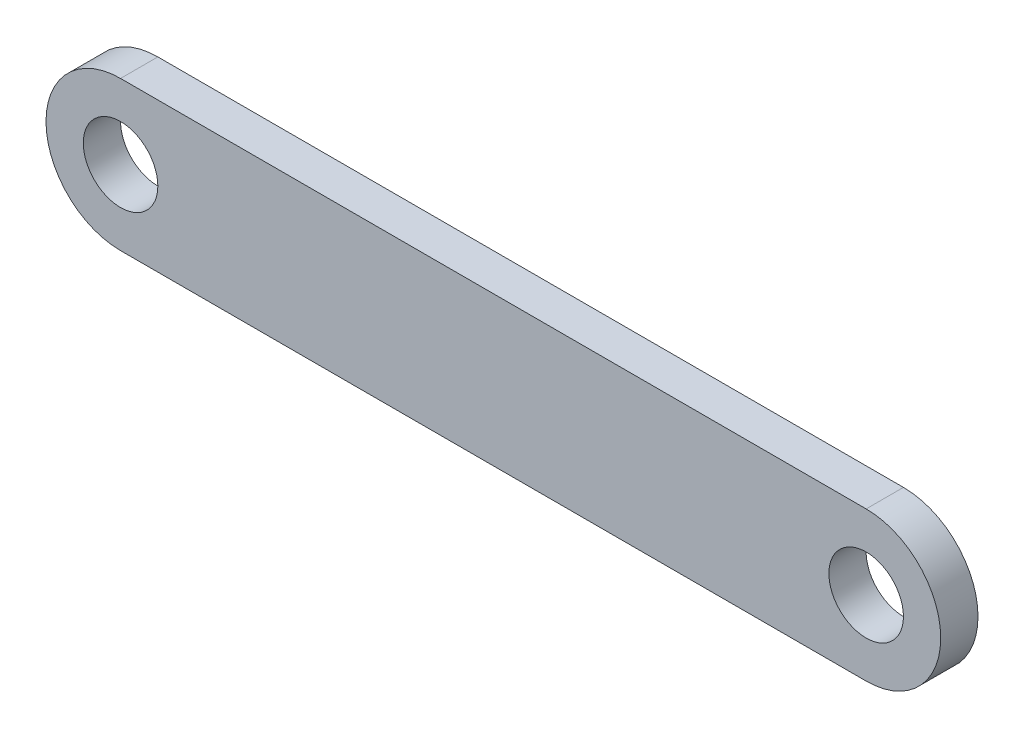
SolidWorks part; units mm, degrees
ref_plane "Front Plane" through (0, 0, 0) normal (0, 0, 1) x (1, 0, 0)
ref_plane "Top Plane" through (0, 0, 0) normal (0, 1, 0) x (1, 0, 0)
ref_plane "Right Plane" through (0, 0, 0) normal (1, 0, 0) x (0, 0, -1)
sketch "Sketch1" plane through (0, 0, 0) normal (0, 0, 1) x (1, 0, 0)
  line L0 (0, 0) -> (100, 0) construction
  line L1 (0, 10) -> (100, 10)
  line L2 (0, -10) -> (100, -10)
  arc A0 (0, 10) -> (0, -10) centre (0, 0) ccw
  arc A1 (100, -10) -> (100, 10) centre (100, 0) ccw
  circle A2 centre (0, 0) radius 5
  circle A3 centre (100, 0) radius 5
  point P3 (50, 0)
  dimension "D1" = 10
  dimension "D3" = 10
  dimension "D4" = 10
  dimension "D2" = 100
extrude "Boss-Extrude1" add sketch "Sketch1" along normal blind 5
